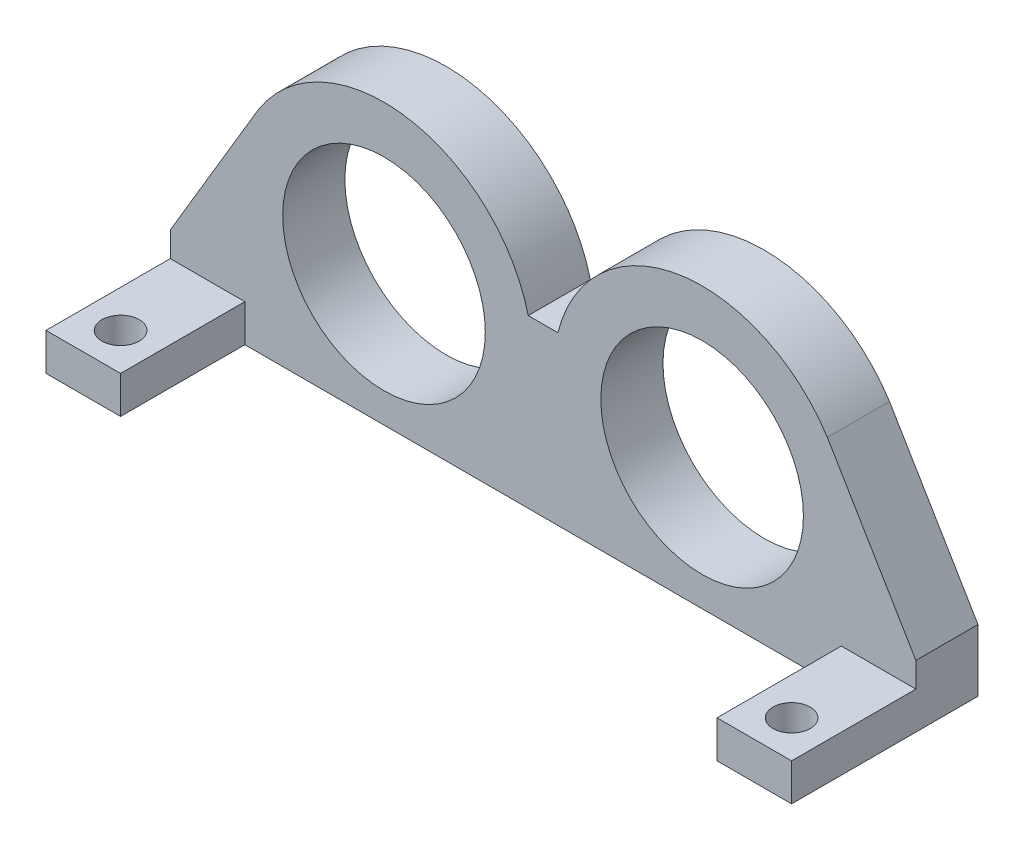
SolidWorks part; units mm, degrees
ref_plane "Front" through (0, 0, 0) normal (0, 0, 1) x (1, 0, 0)
ref_plane "Top" through (0, 0, 0) normal (0, 1, 0) x (1, 0, 0)
ref_plane "Right" through (0, 0, 0) normal (1, 0, 0) x (0, 0, -1)
sketch "Sketch1" plane through (0, 0, 0) normal (0, 0, 1) x (1, 0, 0)
  line L0 (30, 0) -> (-30, 0)
  line L1 (-30, 0) -> (-30, 5)
  line L2 (-30, 5) -> (-22.8772, 16.985)
  line L3 (-1.1933, 13.4339) -> (1.1933, 13.4339)
  line L4 (0, 35.1636) -> (0, -9.6944) construction
  line L5 (30, 5) -> (22.8772, 16.985)
  line L6 (30, 0) -> (30, 5)
  arc A0 (-22.8772, 16.985) -> (-1.1933, 13.4339) centre (-12.8, 10.5397) cw
  circle A1 centre (-12.8, 10.5397) radius 8.15
  circle A2 centre (12.8, 10.5397) radius 8.15
  arc A3 (22.8772, 16.985) -> (1.1933, 13.4339) centre (12.8, 10.5397) ccw
  point P0 (-22.8772, 14.985)
  point P21 (0, 13.4339)
  point P23 (0, 0)
  dimension "D1" = 16.3
  dimension "D2" = 12.8
  dimension "D3" = 60
  dimension "D4" = 5
extrude "Boss-Extrude1" add sketch "Sketch1" along normal blind 5
sketch "Sketch3" plane through (0, 0, 5) normal (0, 0, 1) x (1, 0, 0)
  line L0 (0, 24.744) -> (0, -26.2523) construction
  line L1 (-30, 0) -> (-24, 0)
  line L2 (-30, 0) -> (-30, 3)
  line L3 (-30, 3) -> (-24, 3)
  line L4 (-24, 0) -> (-24, 3)
  line L5 (24, 0) -> (24, 3)
  line L6 (30, 3) -> (24, 3)
  line L7 (30, 0) -> (30, 3)
  line L8 (30, 0) -> (24, 0)
  dimension "D1" = 3
  dimension "D2" = 6
extrude "Boss-Extrude2" add sketch "Sketch3" along normal blind 10
sketch "Sketch4" plane through (0, 3, 0) normal (0, 1, 0) x (1, 0, 0)
  line L1 (-24, -15) -> (-30, -15) construction
  line L2 (30, -15) -> (24, -15) construction
  circle A0 centre (-27, -12) radius 1.5
  circle A1 centre (27, -12) radius 1.5
  point P8 (-27, -15)
  point P9 (27, -15)
  dimension "D1" = 3
  dimension "D2" = 3
  dimension "D3" = 3
  dimension "D4" = 3
extrude "Cut-Extrude1" cut sketch "Sketch4" against normal blind 10
